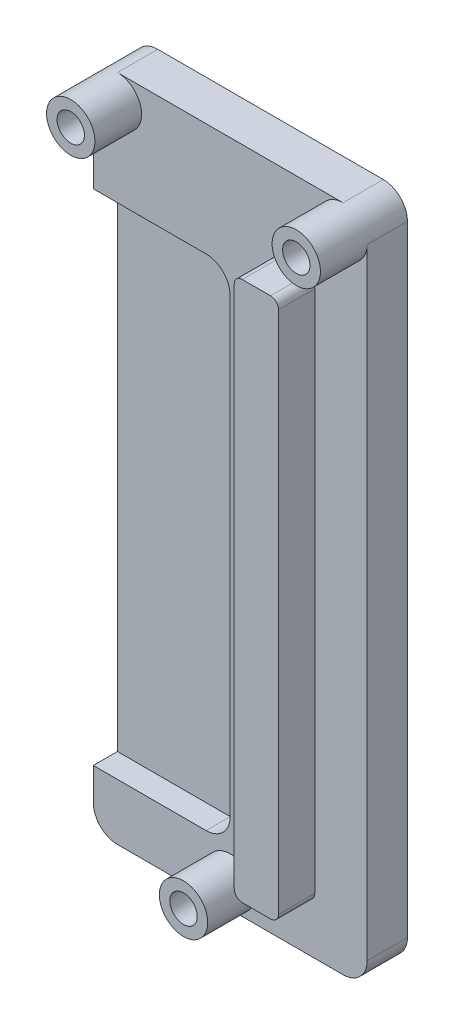
SolidWorks part; units mm, degrees
ref_plane "Plan de face" through (0, 0, 0) normal (0, 0, 1) x (1, 0, 0)
ref_plane "Plan de dessus" through (0, 0, 0) normal (0, 1, 0) x (1, 0, 0)
ref_plane "Plan de droite" through (0, 0, 0) normal (1, 0, 0) x (0, 0, -1)
sketch "Esquisse1" plane through (0, 0, 0) normal (0, 0, 1) x (1, 0, 0)
  line L1 (3, 0) -> (31, 0)
  line L2 (0, 3) -> (0, 80)
  line L3 (3, 83) -> (31, 83)
  line L4 (34, 3) -> (34, 80)
  arc A7 (3, 0) -> (0, 3) centre (3, 3) cw
  arc A8 (31, 0) -> (34, 3) centre (31, 3) ccw
  arc A9 (34, 80) -> (31, 83) centre (31, 80) ccw
  arc A10 (0, 80) -> (3, 83) centre (3, 80) cw
  point P2 (0, 0)
  point P7 (0, 0)
  point P9 (34, 0)
  point P10 (34, 0)
  point P15 (0, 83)
  point P18 (0, 83)
  dimension "D3" = 3
  dimension "D1" = 83
  dimension "D2" = 34
extrude "Boss.-Extru.2" add sketch "Esquisse1" along normal blind 5
sketch "Esquisse4" plane through (0, 0, 5) normal (0, 0, 1) x (1, 0, 0)
  line L0 (0, 80) -> (0, 3) construction
  line L3 (34, 3) -> (34, 80) construction
  line L4 (31, 83) -> (3, 83) construction
  circle A0 centre (3, 80) radius 3
  circle A1 centre (31, 80) radius 3
  circle A2 centre (17, 3) radius 3
  dimension "D1" = 17
  dimension "D2" = 77
  dimension "D3" = 28
  dimension "D4" = 3
  dimension "D5" = 3
  dimension "D6" = 3
extrude "Boss.-Extru.3" add sketch "Esquisse4" along normal blind 5.8
hole_wizard "Dégagement M31" positions "Esquisse5" profile "Esquisse6" hole size "M3" standard "ISO" end condition through all
sketch "Esquisse5" plane through (0, 0, 10.8) normal (0, 0, 1) x (1, 0, 0)
  point P0 (3, 80)
  point P3 (31, 80)
  point P6 (17, 3)
sketch "Esquisse6" plane through (3, 80, 10.8) normal (1, 0, 0) x (0, -1, 0)
  line L0 (0, 0) -> (0, 10.8)
  line L1 (0, 10.8) -> (1.7, 10.8)
  line L2 (1.7, 10.8) -> (1.7, 0)
  line L5 (1.7, 0) -> (0, 0)
  line L11 (0, -6.35) -> (0, 107.95) construction
  dimension "Diamètre du perçage jusqu'au prochain" = 3.4
  dimension "Profondeur du perçage jusqu'au prochain" = 10.8
sketch "Esquisse2" plane through (0, 0, 5) normal (0, 0, 1) x (1, 0, 0)
  line L1 (23, 73) -> (26.5, 73)
  line L2 (22, 72) -> (22, 7)
  line L3 (23, 6) -> (26.5, 6)
  line L4 (27.5, 72) -> (27.5, 7)
  line L9 (31, 83) -> (3, 83) construction
  line L10 (34, 3) -> (34, 80) construction
  arc A2 (22, 7) -> (23, 6) centre (23, 7) ccw
  arc A3 (26.5, 6) -> (27.5, 7) centre (26.5, 7) ccw
  arc A4 (26.5, 73) -> (27.5, 72) centre (26.5, 72) cw
  arc A5 (23, 73) -> (22, 72) centre (23, 72) ccw
  point P25 (24.75, 6)
  dimension "D1" = 6.5
  dimension "D3" = 67
  dimension "D7" = 5.5
  dimension "D8" = 10
extrude "Boss.-Extru.4" add sketch "Esquisse2" along normal blind 4.5
sketch "Esquisse7" plane through (0, 0, 5) normal (0, 0, 1) x (1, 0, 0)
  line L0 (31, 83) -> (3, 83) construction
  line L1 (14, 69) -> (0, 69)
  line L2 (17, 66) -> (17, 10)
  line L3 (14, 7) -> (0, 7)
  line L4 (0, 69) -> (0, 7)
  line L5 (22, 72) -> (22, 7) construction
  arc A1 (17, 10) -> (14, 7) centre (14, 10) cw
  arc A2 (14, 69) -> (17, 66) centre (14, 66) cw
  point P1 (0, 7)
  point P3 (0, 69)
  point P9 (0, 68.9234)
  point P10 (0, 7)
  point P13 (17, 7)
  point P18 (0, 69)
  point P19 (0, 7.1472)
  dimension "D1" = 14
  dimension "D2" = 5
  dimension "D3" = 62
  dimension "D4" = 17
extrude "Enlèv. mat.-Extru.1" cut sketch "Esquisse7" against normal blind 3
